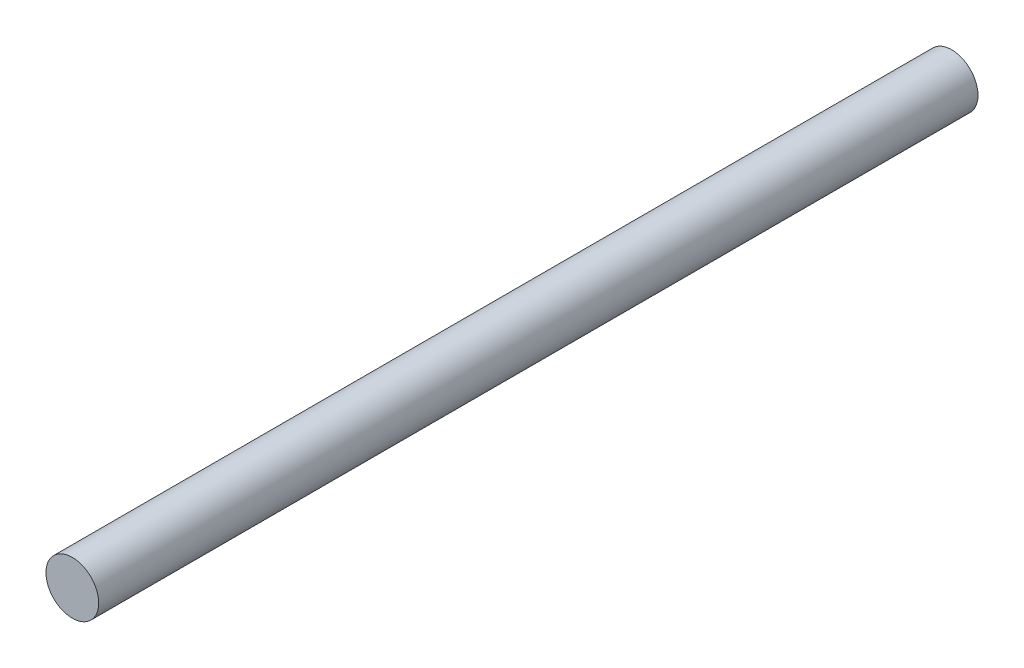
SolidWorks part; units mm, degrees
ref_plane "Front Plane" through (0, 0, 0) normal (0, 0, 1) x (1, 0, 0)
ref_plane "Top Plane" through (0, 0, 0) normal (0, 1, 0) x (1, 0, 0)
ref_plane "Right Plane" through (0, 0, 0) normal (1, 0, 0) x (0, 0, -1)
sketch "Sketch1" plane through (0, 0, 0) normal (0, 0, 1) x (1, 0, 0)
  circle A0 centre (-327.5, 138.0647) radius 3
extrude "Boss-Extrude1" add sketch "Sketch1" along normal blind 100
sketch "Sketch2" plane through (0, 0, 100) normal (0, 0, 1) x (1, 0, 0)
  line L0 (-327.5, 141.0647) -> (-327.5, 135.0647) construction
  circle A0 centre (-327.5, 138.0647) radius 3 construction
sketch "Sketch3" plane through (0, 0, 100) normal (0, 0, 1) x (1, 0, 0)
  line L0 (-327.5, 141.0647) -> (-327.5, 135.0647) construction
  circle A0 centre (-327.5, 138.0647) radius 3 construction
sketch "Sketch4" plane through (0, 0, 100) normal (0, 0, 1) x (1, 0, 0)
  line L0 (-330.5, 138.0647) -> (-324.5, 138.0647) construction
  circle A0 centre (-327.5, 138.0647) radius 3 construction
